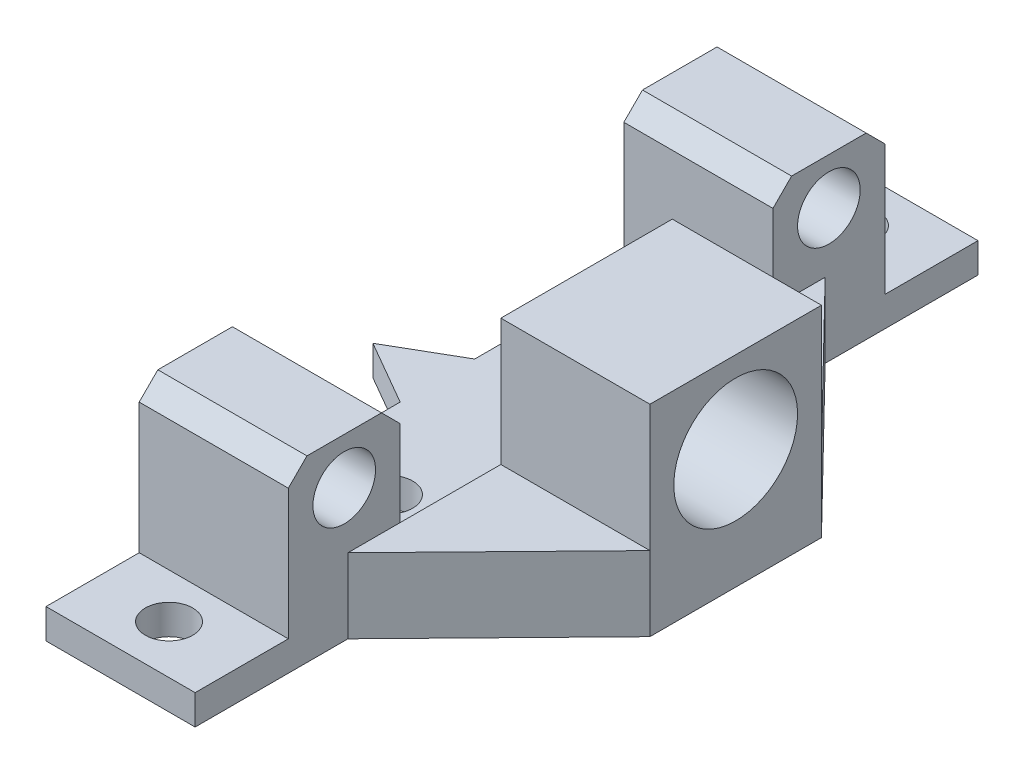
SolidWorks part; units mm, degrees
ref_plane "Front Plane" through (0, 0, 0) normal (0, 0, 1) x (1, 0, 0)
ref_plane "Top Plane" through (0, 0, 0) normal (0, 1, 0) x (1, 0, 0)
ref_plane "Right Plane" through (0, 0, 0) normal (1, 0, 0) x (0, 0, -1)
sketch "Sketch1" plane through (0, 0, 0) normal (0, 1, 0) x (1, 0, 0)
  line L1 (0, 0) -> (20, 0)
  line L2 (0, 0) -> (0, 105)
  line L3 (0, 105) -> (20, 105)
  line L4 (20, 0) -> (20, 105)
  dimension "D1" = 105
  dimension "D2" = 20
extrude "Boss-Extrude1" add sketch "Sketch1" along normal blind 4
sketch "Sketch2" plane through (0, 0, 0) normal (-1, 0, 0) x (0, 0, 1)
  line L0 (-105, 0) -> (0, 0) construction
  line L5 (-12.5, 21.5) -> (-15, 24)
  line L6 (-92.5, 0) -> (-77.5, 0)
  line L7 (-92.5, 0) -> (-92.5, 24)
  line L8 (-92.5, 24) -> (-77.5, 24)
  line L9 (-77.5, 0) -> (-77.5, 24)
  line L10 (-105, 0) -> (-92.5, 0) construction
  line L11 (-80, 24) -> (-77.5, 21.5)
  line L12 (-92.5, 21.5) -> (-90, 24)
  line L13 (-52.5, 0) -> (-52.5, 4) construction
  line L14 (-25, 24) -> (-27.5, 21.5)
  line L15 (-105, 4) -> (0, 4) construction
  line L16 (-27.5, 0) -> (-27.5, 24)
  line L17 (-12.5, 24) -> (-27.5, 24)
  line L18 (-12.5, 0) -> (-12.5, 24)
  line L19 (-12.5, 0) -> (-27.5, 0)
  circle A0 centre (-85, 17.8) radius 4.2
  circle A1 centre (-20, 17.8) radius 4.2
  point P10 (-85, 24)
  point P25 (-52.5, 4)
  point P30 (-20, 24)
  line M15 (0, 4) -> (-105, 4)
  dimension "D4" = 8.4
  dimension "D2" = 15
  dimension "D3" = 24
  dimension "D6" = 2.5
  dimension "D7" = 2.5
  dimension "D8" = 2.5
  dimension "D9" = 2.5
  dimension "D1" = 65
  dimension "D5" = 6.2
extrude "Boss-Extrude2" add sketch "Sketch2" against normal up to surface (20 mm away) contours L18 L5 L17 L14 L16 A1 M15 | L12 L7 L9 L11 L8 A0 M15 up to face at (20, 2, -52.5)
sketch "Sketch3" plane through (0, 0, 0) normal (0, -1, 0) x (1, 0, 0)
  line L0 (0, -57.5) -> (-8.6603, -52.5)
  line L1 (0, -105) -> (0, 0) construction
  line L2 (-8.6603, -52.5) -> (0, -47.5)
  line L3 (0, -57.5) -> (0, -47.5)
  point P6 (0, -52.5)
  dimension "D1" = 10
  dimension "D2" = 10
  dimension "D3" = 10
extrude "Boss-Extrude3" add sketch "Sketch3" against normal up to surface (4 mm away) up to face at (10, 4, -98.75)
sketch "Sketch4" plane through (0, 4, 0) normal (0, 1, 0) x (1, 0, 0)
  line L0 (10, 105) -> (10, 0) construction
  line L1 (20, 105) -> (0, 105) construction
  line L2 (0, 0) -> (20, 0) construction
  circle A0 centre (10, 98.5) radius 3.175
  circle A1 centre (10, 69) radius 3.175
  circle A2 centre (10, 36) radius 3.175
  circle A3 centre (10, 6.5) radius 3.175
  dimension "D1" = 6.35
  dimension "D2" = 6.5
  dimension "D3" = 36
  dimension "D4" = 6.5
  dimension "D5" = 36
extrude "Cut-Extrude1" cut sketch "Sketch4" against normal through all
sketch "Sketch5" plane through (20, 0, 0) normal (1, 0, 0) x (0, 0, -1)
  line L0 (0, 0) -> (105, 0) construction
  line L1 (41, 0) -> (64, 0)
  line L2 (41, 0) -> (41, 27)
  line L3 (41, 27) -> (64, 27)
  line L4 (64, 0) -> (64, 27)
  line L5 (64, 0) -> (105, 0) construction
  line L11 (15, 24) -> (90, 24) construction
  line L12 (41, 0) -> (0, 0) construction
  dimension "D1" = 23
  dimension "D2" = 3
extrude "Boss-Extrude4" add sketch "Sketch5" along normal blind 20
sketch "Sketch6" plane through (40, 0, 0) normal (1, 0, 0) x (0, 0, -1)
  line L0 (52.5, 27) -> (52.5, 0) construction
  line L1 (64, 27) -> (41, 27) construction
  line L2 (41, 0) -> (64, 0) construction
  circle A0 centre (52.5, 16) radius 8.3
  dimension "D1" = 16.6
  dimension "D2" = 11
extrude "Cut-Extrude2" cut sketch "Sketch6" against normal through all
sketch "Sketch11" plane through (0, 0, 0) normal (0, -1, 0) x (1, 0, 0)
  line L0 (40, -64) -> (20, -84.5)
  line L1 (20, -64) -> (20, -105) construction
  line L2 (40, -64) -> (20, -64)
  line L3 (20, -64) -> (20, -84.5)
  line L4 (40, -41) -> (20, -41)
  line L5 (20, -41) -> (20, -20.5)
  line L7 (20, -20.5) -> (40, -41)
  line L8 (20, 0) -> (20, -41) construction
extrude "Boss-Extrude5" add sketch "Sketch11" against normal blind 10
equation "\"8mm hole\" = 8.4mm"
equation "\"D4@Sketch2\"= \"8mm hole\""
equation "\"22mm hole\"= 23mm"
equation "\"15mm hole\"= 15.8mm"
equation "\"bed height offset\"= 3mm"
equation "\"D3@Sketch2\"= 21 + \"bed height offset\""
